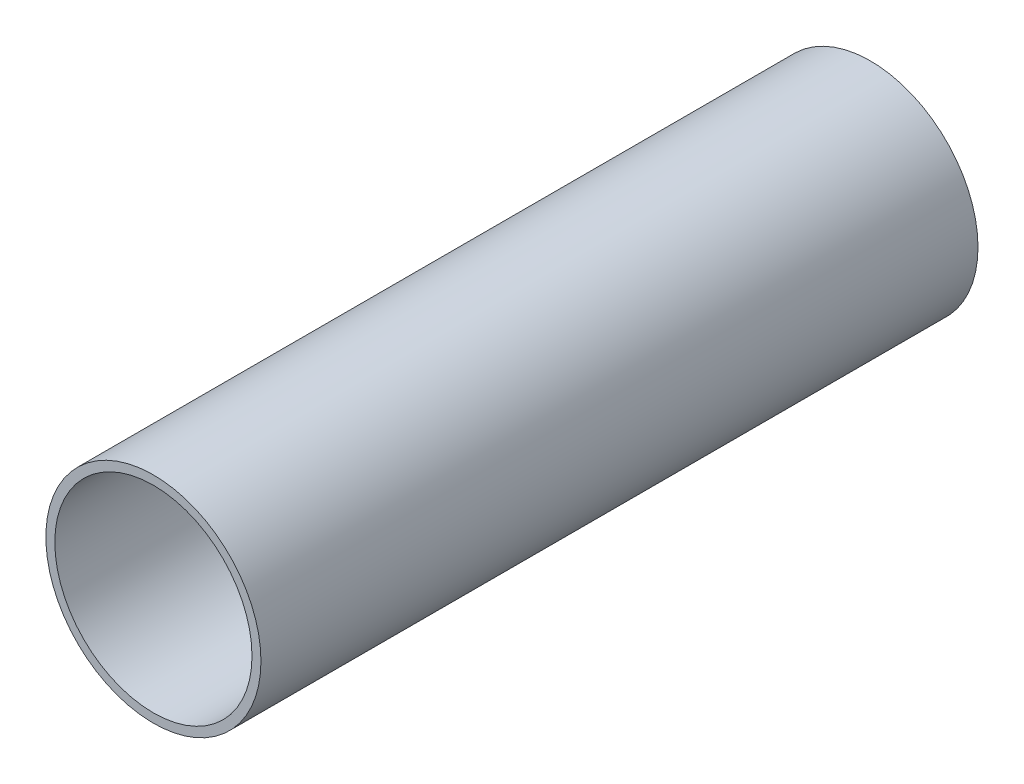
SolidWorks part; units mm, degrees
ref_plane "Front Plane" through (0, 0, 0) normal (0, 0, 1) x (1, 0, 0)
ref_plane "Top Plane" through (0, 0, 0) normal (0, 1, 0) x (1, 0, 0)
ref_plane "Right Plane" through (0, 0, 0) normal (1, 0, 0) x (0, 0, -1)
sketch "Sketch2" plane through (0, 0, 0) normal (0, 0, 1) x (1, 0, 0)
  circle A0 centre (0, 0) radius 38.1
  circle A1 centre (0, 0) radius 34.925
  dimension "D1" = 76.2
  dimension "D2" = 69.85
extrude "Boss-Extrude1" add sketch "Sketch2" against normal blind 254
